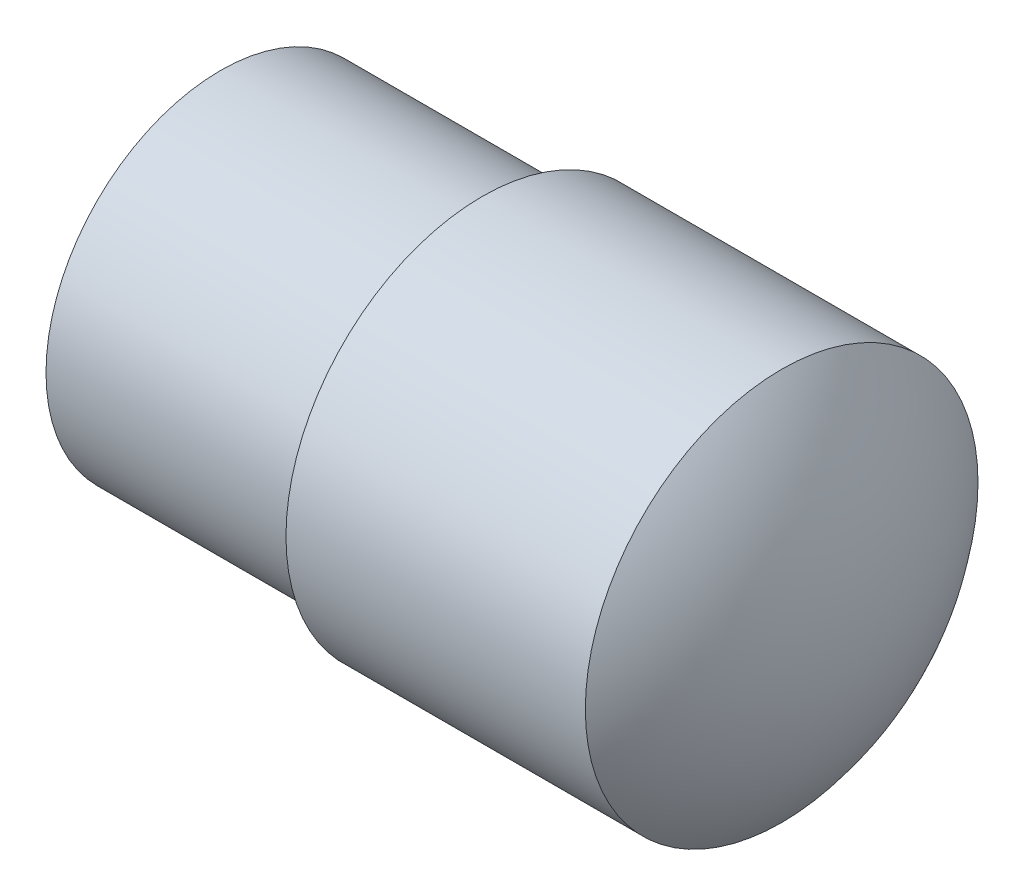
SolidWorks part; units mm, degrees
ref_plane "Face" through (0, 0, 0) normal (0, 0, 1) x (1, 0, 0)
ref_plane "Dessus" through (0, 0, 0) normal (0, 1, 0) x (1, 0, 0)
ref_plane "Droite" through (0, 0, 0) normal (1, 0, 0) x (0, 0, -1)
sketch "Esquisse1" plane through (0, 0, 0) normal (0, 0, 1) x (1, 0, 0)
  line L0 (-129.4124, 0) -> (-100.4124, 0) construction
  line L1 (-117.4124, 9) -> (-103.6886, 9)
  line L2 (-129.4124, 8) -> (-129.4124, 0)
  line L3 (-129.4124, 0) -> (-100.4124, 0)
  line L5 (-117.4124, 9) -> (-117.4124, 8)
  line L6 (-117.4124, 8) -> (-129.4124, 8)
  arc A1 (-100.4124, 0) -> (-103.6886, 9) centre (-114.4124, 0) ccw
revolve "Révolution1" add sketch "Esquisse1" angle 360 about L0
sketch "Esquisse2" plane through (0, 0, 0) normal (0, 0, 1) x (1, 0, 0)
  line L0 (-109.4124, -10.8437) -> (-106.4124, -10.8437)
  line L1 (-106.4124, -10.8437) -> (-106.4124, 0)
  line L3 (-109.4124, 0) -> (-109.4124, -10.8437)
  line L4 (-109.4124, 10.6894) -> (-109.4124, -14.3948) construction
  line L5 (-109.4124, 0) -> (-109.4124, 3)
  line L6 (-117.4124, 9) -> (-117.4124, -9) construction
  arc A0 (-106.4124, 0) -> (-109.4124, 3) centre (-109.4124, 0) ccw
  dimension "D1" = 3
  dimension "D2" = 8
revolve "Enlèvement de matière-Révolution1" cut sketch "Esquisse2" angle 360 about L4
